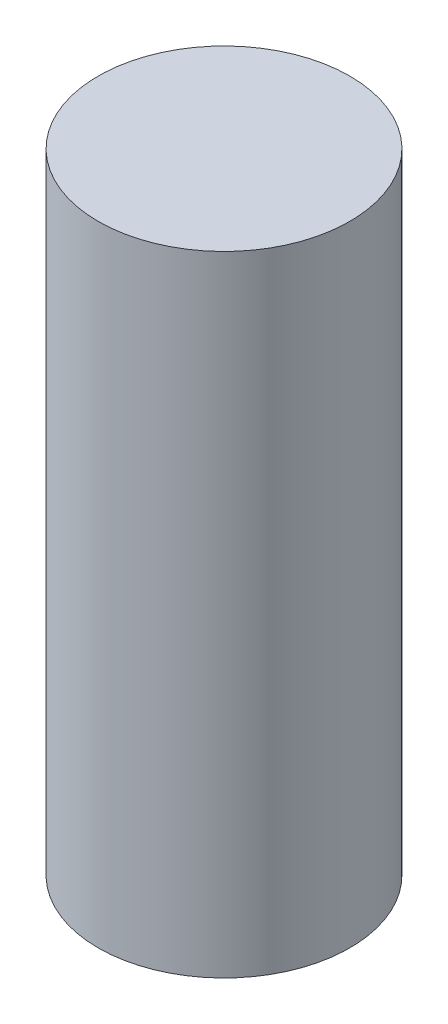
SolidWorks part; units mm, degrees
ref_plane "Front Plane" through (0, 0, 0) normal (0, 0, 1) x (1, 0, 0)
ref_plane "Top Plane" through (0, 0, 0) normal (0, 1, 0) x (1, 0, 0)
ref_plane "Right Plane" through (0, 0, 0) normal (1, 0, 0) x (0, 0, -1)
sketch "Sketch1" plane through (0, 0, 0) normal (0, 1, 0) x (1, 0, 0)
  circle A0 centre (0, 0) radius 2.5
  dimension "D1" = 5
extrude "Boss-Extrude1" add sketch "Sketch1" along normal blind 12.5
